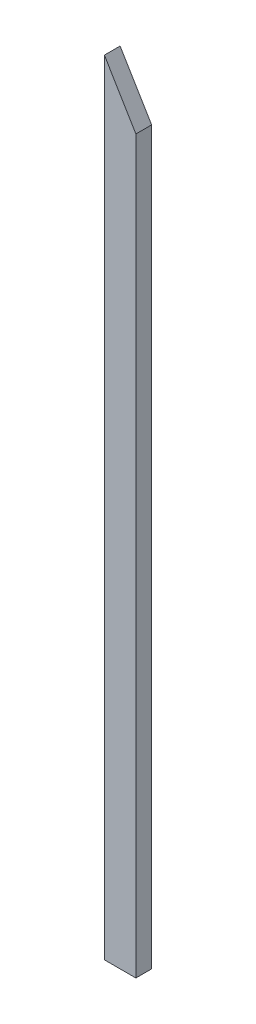
SolidWorks part; units mm, degrees
material "Cedar"
ref_plane "Front Plane" through (0, 0, 0) normal (0, 0, 1) x (1, 0, 0)
ref_plane "Top Plane" through (0, 0, 0) normal (0, 1, 0) x (1, 0, 0)
ref_plane "Right Plane" through (0, 0, 0) normal (1, 0, 0) x (0, 0, -1)
sketch "Sketch1" plane through (0, 0, 0) normal (0, 0, 1) x (1, 0, 0)
  line L1 (-65.2207, 377.7718) -> (-27.1207, 377.7718)
  line L2 (-65.2207, 377.7718) -> (-65.2207, -570.8928)
  line L3 (-65.2207, -570.8928) -> (-27.1207, -570.8928)
  line L4 (-27.1207, 377.7718) -> (-27.1207, -570.8928)
  dimension "D1" = 948.6646
  dimension "D2" = 38.1
extrude "Boss-Extrude1" add sketch "Sketch1" along normal blind 19.05
sketch "Sketch2" plane through (0, 0, 19.05) normal (0, 0, 1) x (1, 0, 0)
  line L0 (-65.2207, 377.7718) -> (-27.1207, 314.1113)
  line L1 (-27.1207, -570.8928) -> (-27.1207, 377.7718) construction
  line L2 (-27.1207, 314.1113) -> (-27.1207, 377.7718)
  line L3 (-27.1207, 377.7718) -> (-65.2207, 377.7718)
  line L4 (-65.2207, 377.7718) -> (-65.2207, -570.8928) construction
  dimension "D1" = 30.9
extrude "Cut-Extrude1" cut sketch "Sketch2" against normal through all
